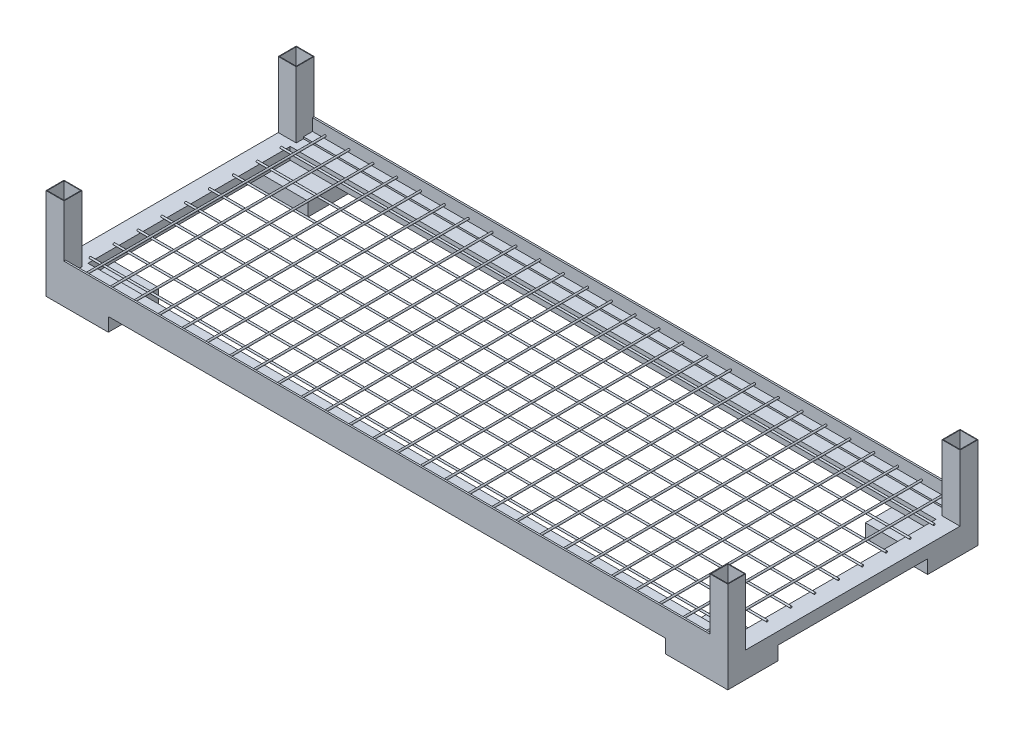
SolidWorks part; units mm, degrees
ref_plane "Front Plane" through (0, 0, 0) normal (0, 0, 1) x (1, 0, 0)
ref_plane "Top Plane" through (0, 0, 0) normal (0, 1, 0) x (1, 0, 0)
ref_plane "Right Plane" through (0, 0, 0) normal (1, 0, 0) x (0, 0, -1)
sketch "Sketch1" plane through (0, 0, 0) normal (0, 1, 0) x (1, 0, 0)
  line L1 (-722.3125, -265.1125) -> (722.3125, -265.1125)
  line L2 (-722.3125, -265.1125) -> (-722.3125, 265.1125)
  line L3 (-722.3125, 265.1125) -> (722.3125, 265.1125)
  line L4 (722.3125, -265.1125) -> (722.3125, 265.1125)
  line L5 (-722.3125, -265.1125) -> (722.3125, 265.1125) construction
  line L6 (-722.3125, 265.1125) -> (722.3125, -265.1125) construction
  line L7 (-684.2125, 214.3125) -> (684.2125, 214.3125)
  line L8 (-684.2125, 214.3125) -> (-684.2125, -214.3125)
  line L9 (-684.2125, -214.3125) -> (684.2125, -214.3125)
  line L10 (684.2125, 214.3125) -> (684.2125, -214.3125)
  line L11 (-684.2125, 214.3125) -> (684.2125, -214.3125) construction
  line L12 (-684.2125, -214.3125) -> (684.2125, 214.3125) construction
  point P0 (0, 0)
  dimension "D1" = 1444.625
  dimension "D2" = 530.225
  dimension "D4" = 38.1
  dimension "D5" = 50.8
  dimension "D3" = 38.1
  dimension "D6" = 50.8
extrude "Boss-Extrude1" add sketch "Sketch1" along normal blind 25.4
sketch "Sketch2" plane through (0, 25.4, 0) normal (0, 1, 0) x (1, 0, 0)
  line L0 (721.0425, -228.2825) -> (685.4825, -228.2825)
  line L1 (-722.3125, 265.1125) -> (-684.2125, 265.1125)
  line L2 (-722.3125, 265.1125) -> (-722.3125, 227.0125)
  line L3 (-722.3125, 227.0125) -> (-684.2125, 227.0125)
  line L4 (-684.2125, 265.1125) -> (-684.2125, 227.0125)
  line L5 (-722.3125, -265.1125) -> (-684.2125, -265.1125)
  line L6 (-722.3125, -265.1125) -> (-722.3125, -227.0125)
  line L7 (-722.3125, -227.0125) -> (-684.2125, -227.0125)
  line L8 (-684.2125, -265.1125) -> (-684.2125, -227.0125)
  line L9 (722.3125, -265.1125) -> (684.2125, -265.1125)
  line L10 (722.3125, -265.1125) -> (722.3125, -227.0125)
  line L11 (722.3125, -227.0125) -> (684.2125, -227.0125)
  line L12 (684.2125, -265.1125) -> (684.2125, -227.0125)
  line L13 (722.3125, 265.1125) -> (684.2125, 265.1125)
  line L14 (722.3125, 265.1125) -> (722.3125, 227.0125)
  line L15 (722.3125, 227.0125) -> (684.2125, 227.0125)
  line L16 (684.2125, 265.1125) -> (684.2125, 227.0125)
  line L17 (685.4825, -263.8425) -> (685.4825, -228.2825)
  line L18 (721.0425, -263.8425) -> (685.4825, -263.8425)
  line L19 (721.0425, -263.8425) -> (721.0425, -228.2825)
  line L20 (721.0425, 228.2825) -> (685.4825, 228.2825)
  line L21 (685.4825, 263.8425) -> (685.4825, 228.2825)
  line L22 (721.0425, 263.8425) -> (685.4825, 263.8425)
  line L23 (721.0425, 263.8425) -> (721.0425, 228.2825)
  line L24 (-685.4825, -263.8425) -> (-685.4825, -228.2825)
  line L25 (-721.0425, -228.2825) -> (-685.4825, -228.2825)
  line L26 (-721.0425, -263.8425) -> (-721.0425, -228.2825)
  line L27 (-721.0425, -263.8425) -> (-685.4825, -263.8425)
  line L28 (-685.4825, 263.8425) -> (-685.4825, 228.2825)
  line L29 (-721.0425, 228.2825) -> (-685.4825, 228.2825)
  line L30 (-721.0425, 263.8425) -> (-721.0425, 228.2825)
  line L31 (-721.0425, 263.8425) -> (-685.4825, 263.8425)
  dimension "D1" = 38.1
  dimension "D2" = 38.1
  dimension "D3" = 1.27
extrude "Boss-Extrude2" add sketch "Sketch2" along normal blind 139.7
sketch "Sketch3" plane through (0, 25.4, 0) normal (0, 1, 0) x (1, 0, 0)
  line L0 (684.2125, 265.1125) -> (684.2125, 227.0125) construction
  line L1 (-684.2125, 265.1125) -> (684.2125, 265.1125)
  line L2 (-684.2125, 265.1125) -> (-684.2125, 242.2525)
  line L3 (-684.2125, 242.2525) -> (684.2125, 242.2525)
  line L4 (684.2125, 265.1125) -> (684.2125, 242.2525)
  line L5 (684.2125, -227.0125) -> (684.2125, -265.1125) construction
  line L6 (-684.2125, -265.1125) -> (684.2125, -265.1125)
  line L7 (-684.2125, -265.1125) -> (-684.2125, -242.2525)
  line L8 (-684.2125, -242.2525) -> (684.2125, -242.2525)
  line L9 (684.2125, -265.1125) -> (684.2125, -242.2525)
  dimension "D1" = 22.86
extrude "Boss-Extrude3" add sketch "Sketch3" along normal blind 3.81
ref_plane "Plane1" through (-690.5625, 0, 0) normal (1, 0, 0) x (0, 0, -1)
sketch "Sketch4" plane through (-690.5625, 0, 0) normal (1, 0, 0) x (0, 0, -1)
  line L0 (227.0125, 25.4) -> (-227.0125, 25.4) construction
  circle A0 centre (-1.3181, 27.305) radius 1.905
  circle A1 centre (49.2279, 27.305) radius 1.905
  circle A2 centre (99.7739, 27.305) radius 1.905
  circle A3 centre (150.3199, 27.305) radius 1.905
  circle A4 centre (200.8659, 27.305) radius 1.905
  circle A5 centre (-51.8641, 27.305) radius 1.905
  circle A6 centre (-102.4101, 27.305) radius 1.905
  circle A7 centre (-152.9561, 27.305) radius 1.905
  circle A8 centre (-203.5021, 27.305) radius 1.905
  dimension "D1" = 1.905
  dimension "D2" = 3.81
  dimension "D3" = 5
  dimension "D4" = 5
extrude "Boss-Extrude4" add sketch "Sketch4" along normal blind 1384.3 separate body
sketch "Sketch5" plane through (0, 29.21, 0) normal (0, 1, 0) x (1, 0, 0)
  line L0 (-684.2125, -265.1125) -> (-684.2125, -227.0125) construction
  line L1 (684.2125, -265.1125) -> (-684.2125, -265.1125)
  line L2 (684.2125, -265.1125) -> (684.2125, -261.5565)
  line L3 (684.2125, -261.5565) -> (-684.2125, -261.5565)
  line L4 (-684.2125, -265.1125) -> (-684.2125, -261.5565)
  line L5 (-684.2125, 227.0125) -> (-684.2125, 265.1125) construction
  line L6 (684.2125, 265.1125) -> (-684.2125, 265.1125)
  line L7 (684.2125, 265.1125) -> (684.2125, 261.5565)
  line L8 (684.2125, 261.5565) -> (-684.2125, 261.5565)
  line L9 (-684.2125, 265.1125) -> (-684.2125, 261.5565)
  dimension "D1" = 3.556
extrude "Boss-Extrude5" add sketch "Sketch5" along normal blind 25.4
sketch "Sketch6" plane through (0, 0, 261.5565) normal (0, 0, -1) x (-1, 0, 0)
  line L0 (-684.2125, 29.21) -> (684.2125, 29.21) construction
  circle A0 centre (0, 34.925) radius 1.905
  circle A1 centre (50.546, 34.925) radius 1.905
  circle A2 centre (101.092, 34.925) radius 1.905
  circle A3 centre (151.638, 34.925) radius 1.905
  circle A4 centre (202.184, 34.925) radius 1.905
  circle A5 centre (252.73, 34.925) radius 1.905
  circle A6 centre (303.276, 34.925) radius 1.905
  circle A7 centre (353.822, 34.925) radius 1.905
  circle A8 centre (404.368, 34.925) radius 1.905
  circle A9 centre (454.914, 34.925) radius 1.905
  circle A10 centre (505.46, 34.925) radius 1.905
  circle A11 centre (556.006, 34.925) radius 1.905
  circle A12 centre (606.552, 34.925) radius 1.905
  circle A13 centre (657.098, 34.925) radius 1.905
  circle A14 centre (0, 34.925) radius 1.905
  circle A15 centre (50.546, 34.925) radius 1.905
  circle A16 centre (101.092, 34.925) radius 1.905
  circle A17 centre (151.638, 34.925) radius 1.905
  circle A18 centre (202.184, 34.925) radius 1.905
  circle A19 centre (252.73, 34.925) radius 1.905
  circle A20 centre (303.276, 34.925) radius 1.905
  circle A21 centre (353.822, 34.925) radius 1.905
  circle A22 centre (404.368, 34.925) radius 1.905
  circle A23 centre (454.914, 34.925) radius 1.905
  circle A24 centre (505.46, 34.925) radius 1.905
  circle A25 centre (556.006, 34.925) radius 1.905
  circle A26 centre (606.552, 34.925) radius 1.905
  circle A27 centre (-50.546, 34.925) radius 1.905
  circle A28 centre (0, 34.925) radius 1.905
  circle A29 centre (50.546, 34.925) radius 1.905
  circle A30 centre (101.092, 34.925) radius 1.905
  circle A31 centre (151.638, 34.925) radius 1.905
  circle A32 centre (202.184, 34.925) radius 1.905
  circle A33 centre (252.73, 34.925) radius 1.905
  circle A34 centre (303.276, 34.925) radius 1.905
  circle A35 centre (353.822, 34.925) radius 1.905
  circle A36 centre (404.368, 34.925) radius 1.905
  circle A37 centre (454.914, 34.925) radius 1.905
  circle A38 centre (505.46, 34.925) radius 1.905
  circle A39 centre (556.006, 34.925) radius 1.905
  circle A40 centre (-101.092, 34.925) radius 1.905
  circle A41 centre (-50.546, 34.925) radius 1.905
  circle A42 centre (0, 34.925) radius 1.905
  circle A43 centre (50.546, 34.925) radius 1.905
  circle A44 centre (101.092, 34.925) radius 1.905
  circle A45 centre (151.638, 34.925) radius 1.905
  circle A46 centre (202.184, 34.925) radius 1.905
  circle A47 centre (252.73, 34.925) radius 1.905
  circle A48 centre (303.276, 34.925) radius 1.905
  circle A49 centre (353.822, 34.925) radius 1.905
  circle A50 centre (404.368, 34.925) radius 1.905
  circle A51 centre (454.914, 34.925) radius 1.905
  circle A52 centre (505.46, 34.925) radius 1.905
  circle A53 centre (-151.638, 34.925) radius 1.905
  circle A54 centre (-101.092, 34.925) radius 1.905
  circle A55 centre (-50.546, 34.925) radius 1.905
  circle A56 centre (0, 34.925) radius 1.905
  circle A57 centre (50.546, 34.925) radius 1.905
  circle A58 centre (101.092, 34.925) radius 1.905
  circle A59 centre (151.638, 34.925) radius 1.905
  circle A60 centre (202.184, 34.925) radius 1.905
  circle A61 centre (252.73, 34.925) radius 1.905
  circle A62 centre (303.276, 34.925) radius 1.905
  circle A63 centre (353.822, 34.925) radius 1.905
  circle A64 centre (404.368, 34.925) radius 1.905
  circle A65 centre (454.914, 34.925) radius 1.905
  circle A66 centre (-202.184, 34.925) radius 1.905
  circle A67 centre (-151.638, 34.925) radius 1.905
  circle A68 centre (-101.092, 34.925) radius 1.905
  circle A69 centre (-50.546, 34.925) radius 1.905
  circle A70 centre (0, 34.925) radius 1.905
  circle A71 centre (50.546, 34.925) radius 1.905
  circle A72 centre (101.092, 34.925) radius 1.905
  circle A73 centre (151.638, 34.925) radius 1.905
  circle A74 centre (202.184, 34.925) radius 1.905
  circle A75 centre (252.73, 34.925) radius 1.905
  circle A76 centre (303.276, 34.925) radius 1.905
  circle A77 centre (353.822, 34.925) radius 1.905
  circle A78 centre (404.368, 34.925) radius 1.905
  circle A79 centre (-252.73, 34.925) radius 1.905
  circle A80 centre (-202.184, 34.925) radius 1.905
  circle A81 centre (-151.638, 34.925) radius 1.905
  circle A82 centre (-101.092, 34.925) radius 1.905
  circle A83 centre (-50.546, 34.925) radius 1.905
  circle A84 centre (0, 34.925) radius 1.905
  circle A85 centre (50.546, 34.925) radius 1.905
  circle A86 centre (101.092, 34.925) radius 1.905
  circle A87 centre (151.638, 34.925) radius 1.905
  circle A88 centre (202.184, 34.925) radius 1.905
  circle A89 centre (252.73, 34.925) radius 1.905
  circle A90 centre (303.276, 34.925) radius 1.905
  circle A91 centre (353.822, 34.925) radius 1.905
  circle A92 centre (-303.276, 34.925) radius 1.905
  circle A93 centre (-252.73, 34.925) radius 1.905
  circle A94 centre (-202.184, 34.925) radius 1.905
  circle A95 centre (-151.638, 34.925) radius 1.905
  circle A96 centre (-101.092, 34.925) radius 1.905
  circle A97 centre (-50.546, 34.925) radius 1.905
  circle A98 centre (0, 34.925) radius 1.905
  circle A99 centre (50.546, 34.925) radius 1.905
  circle A100 centre (101.092, 34.925) radius 1.905
  circle A101 centre (151.638, 34.925) radius 1.905
  circle A102 centre (202.184, 34.925) radius 1.905
  circle A103 centre (252.73, 34.925) radius 1.905
  circle A104 centre (303.276, 34.925) radius 1.905
  circle A105 centre (-353.822, 34.925) radius 1.905
  circle A106 centre (-303.276, 34.925) radius 1.905
  circle A107 centre (-252.73, 34.925) radius 1.905
  circle A108 centre (-202.184, 34.925) radius 1.905
  circle A109 centre (-151.638, 34.925) radius 1.905
  circle A110 centre (-101.092, 34.925) radius 1.905
  circle A111 centre (-50.546, 34.925) radius 1.905
  circle A112 centre (0, 34.925) radius 1.905
  circle A113 centre (50.546, 34.925) radius 1.905
  circle A114 centre (101.092, 34.925) radius 1.905
  circle A115 centre (151.638, 34.925) radius 1.905
  circle A116 centre (202.184, 34.925) radius 1.905
  circle A117 centre (252.73, 34.925) radius 1.905
  circle A118 centre (-404.368, 34.925) radius 1.905
  circle A119 centre (-353.822, 34.925) radius 1.905
  circle A120 centre (-303.276, 34.925) radius 1.905
  circle A121 centre (-252.73, 34.925) radius 1.905
  circle A122 centre (-202.184, 34.925) radius 1.905
  circle A123 centre (-151.638, 34.925) radius 1.905
  circle A124 centre (-101.092, 34.925) radius 1.905
  circle A125 centre (-50.546, 34.925) radius 1.905
  circle A126 centre (0, 34.925) radius 1.905
  circle A127 centre (50.546, 34.925) radius 1.905
  circle A128 centre (101.092, 34.925) radius 1.905
  circle A129 centre (151.638, 34.925) radius 1.905
  circle A130 centre (202.184, 34.925) radius 1.905
  circle A131 centre (-454.914, 34.925) radius 1.905
  circle A132 centre (-404.368, 34.925) radius 1.905
  circle A133 centre (-353.822, 34.925) radius 1.905
  circle A134 centre (-303.276, 34.925) radius 1.905
  circle A135 centre (-252.73, 34.925) radius 1.905
  circle A136 centre (-202.184, 34.925) radius 1.905
  circle A137 centre (-151.638, 34.925) radius 1.905
  circle A138 centre (-101.092, 34.925) radius 1.905
  circle A139 centre (-50.546, 34.925) radius 1.905
  circle A140 centre (0, 34.925) radius 1.905
  circle A141 centre (50.546, 34.925) radius 1.905
  circle A142 centre (101.092, 34.925) radius 1.905
  circle A143 centre (151.638, 34.925) radius 1.905
  circle A144 centre (-505.46, 34.925) radius 1.905
  circle A145 centre (-454.914, 34.925) radius 1.905
  circle A146 centre (-404.368, 34.925) radius 1.905
  circle A147 centre (-353.822, 34.925) radius 1.905
  circle A148 centre (-303.276, 34.925) radius 1.905
  circle A149 centre (-252.73, 34.925) radius 1.905
  circle A150 centre (-202.184, 34.925) radius 1.905
  circle A151 centre (-151.638, 34.925) radius 1.905
  circle A152 centre (-101.092, 34.925) radius 1.905
  circle A153 centre (-50.546, 34.925) radius 1.905
  circle A154 centre (0, 34.925) radius 1.905
  circle A155 centre (50.546, 34.925) radius 1.905
  circle A156 centre (101.092, 34.925) radius 1.905
  circle A157 centre (-556.006, 34.925) radius 1.905
  circle A158 centre (-505.46, 34.925) radius 1.905
  circle A159 centre (-454.914, 34.925) radius 1.905
  circle A160 centre (-404.368, 34.925) radius 1.905
  circle A161 centre (-353.822, 34.925) radius 1.905
  circle A162 centre (-303.276, 34.925) radius 1.905
  circle A163 centre (-252.73, 34.925) radius 1.905
  circle A164 centre (-202.184, 34.925) radius 1.905
  circle A165 centre (-151.638, 34.925) radius 1.905
  circle A166 centre (-101.092, 34.925) radius 1.905
  circle A167 centre (-50.546, 34.925) radius 1.905
  circle A168 centre (0, 34.925) radius 1.905
  circle A169 centre (50.546, 34.925) radius 1.905
  circle A170 centre (-606.552, 34.925) radius 1.905
  circle A171 centre (-556.006, 34.925) radius 1.905
  circle A172 centre (-505.46, 34.925) radius 1.905
  circle A173 centre (-454.914, 34.925) radius 1.905
  circle A174 centre (-404.368, 34.925) radius 1.905
  circle A175 centre (-353.822, 34.925) radius 1.905
  circle A176 centre (-303.276, 34.925) radius 1.905
  circle A177 centre (-252.73, 34.925) radius 1.905
  circle A178 centre (-202.184, 34.925) radius 1.905
  circle A179 centre (-151.638, 34.925) radius 1.905
  circle A180 centre (-101.092, 34.925) radius 1.905
  circle A181 centre (-50.546, 34.925) radius 1.905
  circle A182 centre (0, 34.925) radius 1.905
  circle A183 centre (-50.546, 34.925) radius 1.905
  circle A184 centre (-101.092, 34.925) radius 1.905
  circle A185 centre (-151.638, 34.925) radius 1.905
  circle A186 centre (-202.184, 34.925) radius 1.905
  circle A187 centre (-252.73, 34.925) radius 1.905
  circle A188 centre (-303.276, 34.925) radius 1.905
  circle A189 centre (-353.822, 34.925) radius 1.905
  circle A190 centre (-404.368, 34.925) radius 1.905
  circle A191 centre (-454.914, 34.925) radius 1.905
  circle A192 centre (-505.46, 34.925) radius 1.905
  circle A193 centre (-556.006, 34.925) radius 1.905
  circle A194 centre (-606.552, 34.925) radius 1.905
  circle A195 centre (-657.098, 34.925) radius 1.905
  dimension "D1" = 3.81
  dimension "D2" = 5.715
  dimension "D3" = 14
  dimension "D4" = 14
extrude "Boss-Extrude6" add sketch "Sketch6" along normal blind 523.113
sketch "Sketch7" plane through (0, 0, 0) normal (0, -1, 0) x (1, 0, 0)
  line L1 (-722.3125, -265.1125) -> (-590.2325, -265.1125)
  line L2 (-722.3125, -265.1125) -> (-722.3125, -158.4325)
  line L3 (-722.3125, -158.4325) -> (-590.2325, -158.4325)
  line L4 (-590.2325, -265.1125) -> (-590.2325, -158.4325)
  line L5 (-722.3125, 265.1125) -> (-590.2325, 265.1125)
  line L6 (-722.3125, 265.1125) -> (-722.3125, 158.4325)
  line L7 (-722.3125, 158.4325) -> (-590.2325, 158.4325)
  line L8 (-590.2325, 265.1125) -> (-590.2325, 158.4325)
  line L9 (722.3125, -265.1125) -> (590.2325, -265.1125)
  line L10 (722.3125, -265.1125) -> (722.3125, -158.4325)
  line L11 (722.3125, -158.4325) -> (590.2325, -158.4325)
  line L12 (590.2325, -265.1125) -> (590.2325, -158.4325)
  line L13 (722.3125, 265.1125) -> (590.2325, 265.1125)
  line L14 (722.3125, 265.1125) -> (722.3125, 158.4325)
  line L15 (722.3125, 158.4325) -> (590.2325, 158.4325)
  line L16 (590.2325, 265.1125) -> (590.2325, 158.4325)
  dimension "D1" = 132.08
  dimension "D2" = 106.68
extrude "Boss-Extrude7" add sketch "Sketch7" along normal blind 3.556
sketch "Sketch8" plane through (0, -3.556, 0) normal (0, -1, 0) x (1, 0, 0)
  line L0 (-718.7565, -261.5565) -> (-593.7885, -261.5565)
  line L1 (-722.3125, -265.1125) -> (-590.2325, -265.1125)
  line L2 (-722.3125, -265.1125) -> (-722.3125, -158.4325)
  line L3 (-722.3125, -158.4325) -> (-590.2325, -158.4325)
  line L4 (-590.2325, -265.1125) -> (-590.2325, -158.4325)
  line L5 (-722.3125, 265.1125) -> (-590.2325, 265.1125)
  line L6 (-722.3125, 265.1125) -> (-722.3125, 158.4325)
  line L7 (-722.3125, 158.4325) -> (-590.2325, 158.4325)
  line L8 (-590.2325, 265.1125) -> (-590.2325, 158.4325)
  line L9 (590.2325, 158.4325) -> (722.3125, 158.4325)
  line L10 (590.2325, 158.4325) -> (590.2325, 265.1125)
  line L11 (590.2325, 265.1125) -> (722.3125, 265.1125)
  line L12 (722.3125, 158.4325) -> (722.3125, 265.1125)
  line L13 (590.2325, -158.4325) -> (722.3125, -158.4325)
  line L14 (590.2325, -158.4325) -> (590.2325, -265.1125)
  line L15 (590.2325, -265.1125) -> (722.3125, -265.1125)
  line L16 (722.3125, -158.4325) -> (722.3125, -265.1125)
  line L17 (-593.7885, -261.5565) -> (-593.7885, -161.9885)
  line L18 (-718.7565, -161.9885) -> (-593.7885, -161.9885)
  line L19 (-718.7565, -261.5565) -> (-718.7565, -161.9885)
  line L20 (-718.7565, 261.5565) -> (-593.7885, 261.5565)
  line L21 (-593.7885, 261.5565) -> (-593.7885, 161.9885)
  line L22 (-718.7565, 161.9885) -> (-593.7885, 161.9885)
  line L23 (-718.7565, 261.5565) -> (-718.7565, 161.9885)
  line L24 (593.7885, 161.9885) -> (718.7565, 161.9885)
  line L25 (718.7565, 161.9885) -> (718.7565, 261.5565)
  line L26 (593.7885, 261.5565) -> (718.7565, 261.5565)
  line L27 (593.7885, 161.9885) -> (593.7885, 261.5565)
  line L28 (593.7885, -161.9885) -> (718.7565, -161.9885)
  line L29 (718.7565, -161.9885) -> (718.7565, -261.5565)
  line L30 (593.7885, -261.5565) -> (718.7565, -261.5565)
  line L31 (593.7885, -161.9885) -> (593.7885, -261.5565)
  dimension "D1" = 3.556
extrude "Boss-Extrude8" add sketch "Sketch8" along normal blind 25.4
sketch "Sketch9" plane through (0, 25.4, 0) normal (0, 1, 0) x (1, 0, 0)
  line L1 (-721.0425, 263.8425) -> (-685.4825, 263.8425)
  line L2 (-721.0425, 263.8425) -> (-721.0425, 228.2825)
  line L3 (-721.0425, 228.2825) -> (-685.4825, 228.2825)
  line L4 (-685.4825, 263.8425) -> (-685.4825, 228.2825)
  line L5 (-721.0425, -228.2825) -> (-685.4825, -228.2825)
  line L6 (-721.0425, -228.2825) -> (-721.0425, -263.8425)
  line L7 (-721.0425, -263.8425) -> (-685.4825, -263.8425)
  line L8 (-685.4825, -228.2825) -> (-685.4825, -263.8425)
  line L9 (685.4825, -228.2825) -> (721.0425, -228.2825)
  line L10 (685.4825, -228.2825) -> (685.4825, -263.8425)
  line L11 (685.4825, -263.8425) -> (721.0425, -263.8425)
  line L12 (721.0425, -228.2825) -> (721.0425, -263.8425)
  line L13 (685.4825, 263.8425) -> (721.0425, 263.8425)
  line L14 (685.4825, 263.8425) -> (685.4825, 228.2825)
  line L15 (685.4825, 228.2825) -> (721.0425, 228.2825)
  line L16 (721.0425, 263.8425) -> (721.0425, 228.2825)
extrude "Cut-Extrude1" cut sketch "Sketch9" against normal blind 22.606
